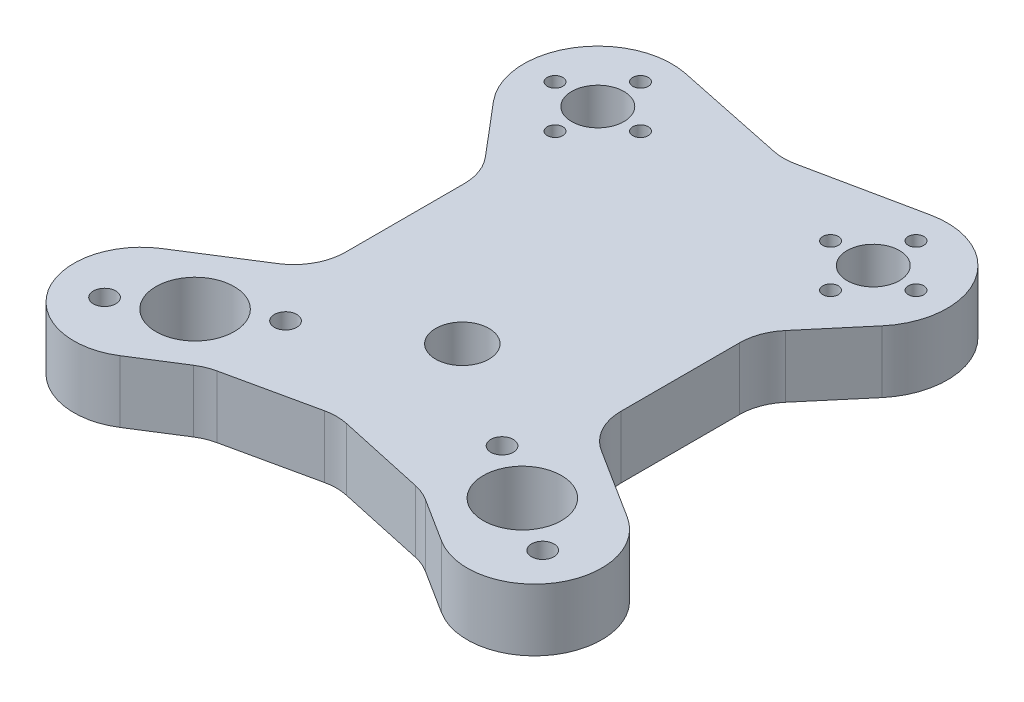
SolidWorks part; units mm, degrees
ref_plane "Front Plane" through (0, 0, 0) normal (0, 0, 1) x (1, 0, 0)
ref_plane "Top Plane" through (0, 0, 0) normal (0, 1, 0) x (1, 0, 0)
ref_plane "Right Plane" through (0, 0, 0) normal (1, 0, 0) x (0, 0, -1)
sketch "Sketch1" plane through (0, 0, 0) normal (0, 1, 0) x (1, 0, 0)
  line L0 (0, -78.0652) -> (0, 78.0652) construction
  line L1 (-42.2865, -26.7721) -> (-20.8935, -13.2279) construction
  line L2 (-2.0365, 62.2326) -> (-23.679, 66.7345)
  line L3 (-37.5049, 43.5105) -> (-28.954, 33.3983)
  line L4 (-26.59, 26.9413) -> (-26.59, 4.037)
  line L5 (-31.2408, -4.412) -> (-44.9142, -13.0688)
  line L6 (-31.0239, -35.0085) -> (-44.9142, -13.0688) construction
  line L7 (-31.0239, -35.0085) -> (-22.3861, -29.5398)
  line L8 (-19.1675, -28.2185) -> (-2.1306, -24.5033)
  line L9 (31.0239, -35.0085) -> (44.9142, -13.0688) construction
  line L10 (42.2865, -26.7721) -> (20.8935, -13.2279) construction
  line L11 (19.1675, -28.2185) -> (2.1306, -24.5033)
  line L12 (31.0239, -35.0085) -> (22.3861, -29.5398)
  line L13 (31.2408, -4.412) -> (44.9142, -13.0688)
  line L14 (26.59, 26.9413) -> (26.59, 4.037)
  line L15 (37.5049, 43.5105) -> (28.954, 33.3983)
  line L16 (2.0365, 62.2326) -> (23.679, 66.7345)
  circle A0 centre (0, 0) radius 5.15
  circle A1 centre (-31.59, -20) radius 7.55
  circle A3 centre (-26.59, 52.74) radius 5.05
  circle A4 centre (-26.59, 52.74) radius 11 construction
  circle A5 centre (-26.59, 52.74) radius 8.25 construction
  circle A6 centre (-26.59, 60.99) radius 1.5
  circle A7 centre (-18.34, 52.74) radius 1.5
  circle A8 centre (-26.59, 44.49) radius 1.5
  circle A9 centre (-34.84, 52.74) radius 1.5
  circle A10 centre (-42.2865, -26.7721) radius 2.165
  circle A11 centre (-20.8935, -13.2279) radius 2.165
  arc A12 (-23.679, 66.7345) -> (-37.5049, 43.5105) centre (-26.59, 52.74) ccw
  arc A13 (-44.9142, -13.0688) -> (-31.0239, -35.0085) centre (-37.969, -24.0386) ccw
  arc A14 (-22.3861, -29.5398) -> (-19.1675, -28.2185) centre (-17.0369, -37.9889) cw
  arc A15 (-28.954, 33.3983) -> (-26.59, 26.9413) centre (-36.59, 26.9413) cw
  arc A16 (-26.59, 4.037) -> (-31.2408, -4.412) centre (-36.59, 4.037) cw
  circle A17 centre (26.59, 52.74) radius 8.25 construction
  circle A18 centre (26.59, 52.74) radius 11 construction
  arc A19 (26.59, 4.037) -> (31.2408, -4.412) centre (36.59, 4.037) ccw
  arc A20 (28.954, 33.3983) -> (26.59, 26.9413) centre (36.59, 26.9413) ccw
  arc A21 (22.3861, -29.5398) -> (19.1675, -28.2185) centre (17.0369, -37.9889) ccw
  arc A22 (44.9142, -13.0688) -> (31.0239, -35.0085) centre (37.969, -24.0386) cw
  arc A23 (23.679, 66.7345) -> (37.5049, 43.5105) centre (26.59, 52.74) cw
  circle A24 centre (20.8935, -13.2279) radius 2.165
  circle A25 centre (42.2865, -26.7721) radius 2.165
  circle A26 centre (34.84, 52.74) radius 1.5
  circle A27 centre (26.59, 44.49) radius 1.5
  circle A28 centre (18.34, 52.74) radius 1.5
  circle A29 centre (26.59, 60.99) radius 1.5
  circle A30 centre (26.59, 52.74) radius 5.05
  circle A31 centre (31.59, -20) radius 7.55
  arc A32 (-2.1306, -24.5033) -> (2.1306, -24.5033) centre (0, -34.2736) cw
  arc A33 (-2.0365, 62.2326) -> (2.0365, 62.2326) centre (0, 72.0231) ccw
  point P10 (0, 0)
  point P23 (-26.59, 52.74)
  point P25 (-31.59, -20)
  point P76 (31.59, -20)
  point P77 (26.59, 52.74)
  point P80 (0, -24.0386)
  point P83 (0, 61.809)
  dimension "D1" = 10.3
  dimension "D2" = 10.1
  dimension "D3" = 3
  dimension "D4" = 15.1
  dimension "D5" = 4
  dimension "D6" = 16.5
  dimension "D7" = 22
  dimension "D9" = 4.33
  dimension "D14" = 10
  dimension "D15" = 10
  dimension "D8" = 25.32
  dimension "D10" = 31.59
  dimension "D11" = 20
  dimension "D12" = 52.74
  dimension "D13" = 26.59
extrude "Boss-Extrude1" add sketch "Sketch1" along normal blind 12
